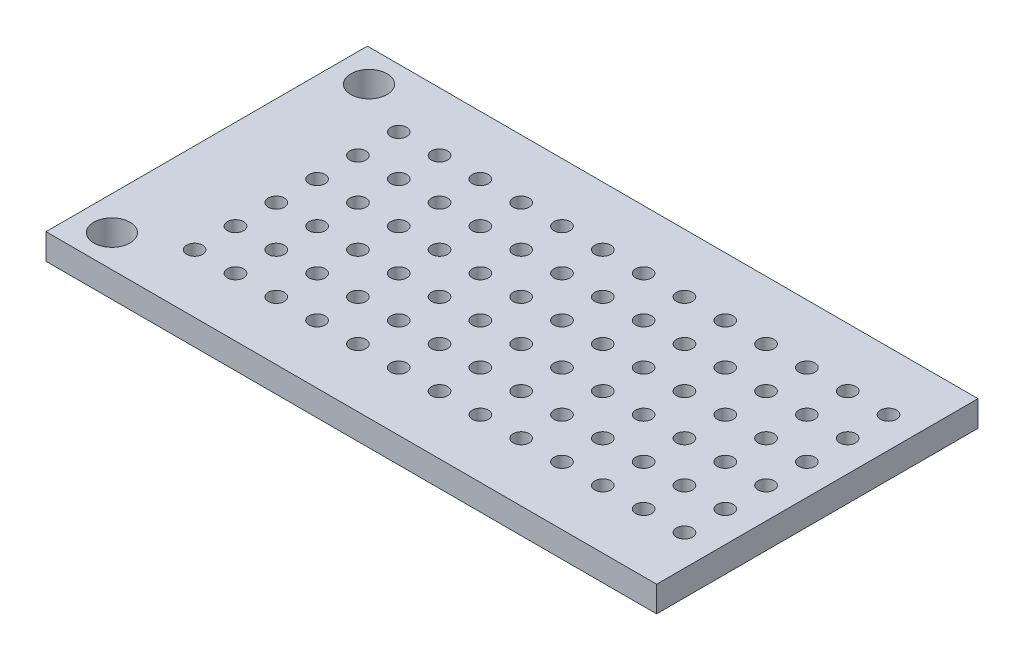
SolidWorks part; units mm, degrees
ref_plane "Front Plane" through (0, 0, 0) normal (0, 0, 1) x (1, 0, 0)
ref_plane "Top Plane" through (0, 0, 0) normal (0, 1, 0) x (1, 0, 0)
ref_plane "Right Plane" through (0, 0, 0) normal (1, 0, 0) x (0, 0, -1)
sketch "Sketch1" plane through (0, 0, 0) normal (0, 1, 0) x (1, 0, 0)
  line L1 (0, 0) -> (38, 0)
  line L2 (0, 0) -> (0, 20)
  line L3 (0, 20) -> (38, 20)
  line L4 (38, 0) -> (38, 20)
  dimension "D1" = 20
  dimension "D2" = 38
extrude "Boss-Extrude1" add sketch "Sketch1" along normal blind 1.6
sketch "Sketch2" plane through (0, 1.6, 0) normal (0, 1, 0) x (1, 0, 0)
  line L0 (2.1, 2) -> (2.1, 0) construction
  line L1 (0, 0) -> (38, 0) construction
  line L2 (2.1, 18) -> (2.1, 20) construction
  line L3 (38, 20) -> (0, 20) construction
  line L4 (0, 20) -> (0, 0) construction
  circle A0 centre (2.1, 18) radius 1.125
  circle A1 centre (2.1, 2) radius 1.125
  dimension "D1" = 2.25
  dimension "D2" = 2.25
  dimension "D3" = 16
  dimension "D4" = 2.1
sketch "Sketch3" plane through (0, 1.6, 0) normal (0, 1, 0) x (1, 0, 0)
  line L0 (0, 20) -> (0, 0) construction
  line L1 (5.6, 16.35) -> (5.6, 20) construction
  line L2 (38, 20) -> (0, 20) construction
  line L3 (5.6, 3.65) -> (5.6, 0) construction
  line L4 (0, 0) -> (38, 0) construction
  circle A0 centre (5.6, 16.35) radius 0.5
  circle A1 centre (8.14, 16.35) radius 0.5
  circle A2 centre (10.68, 16.35) radius 0.5
  circle A3 centre (13.22, 16.35) radius 0.5
  circle A4 centre (15.76, 16.35) radius 0.5
  circle A5 centre (18.3, 16.35) radius 0.5
  circle A6 centre (20.84, 16.35) radius 0.5
  circle A7 centre (23.38, 16.35) radius 0.5
  circle A8 centre (25.92, 16.35) radius 0.5
  circle A9 centre (28.46, 16.35) radius 0.5
  circle A10 centre (31, 16.35) radius 0.5
  circle A11 centre (33.54, 16.35) radius 0.5
  circle A12 centre (36.08, 16.35) radius 0.5
  circle A13 centre (8.14, 13.81) radius 0.5
  circle A14 centre (10.68, 13.81) radius 0.5
  circle A15 centre (13.22, 13.81) radius 0.5
  circle A16 centre (15.76, 13.81) radius 0.5
  circle A17 centre (18.3, 13.81) radius 0.5
  circle A18 centre (20.84, 13.81) radius 0.5
  circle A19 centre (23.38, 13.81) radius 0.5
  circle A20 centre (25.92, 13.81) radius 0.5
  circle A21 centre (28.46, 13.81) radius 0.5
  circle A22 centre (31, 13.81) radius 0.5
  circle A23 centre (33.54, 13.81) radius 0.5
  circle A24 centre (36.08, 13.81) radius 0.5
  circle A25 centre (8.14, 11.27) radius 0.5
  circle A26 centre (10.68, 11.27) radius 0.5
  circle A27 centre (13.22, 11.27) radius 0.5
  circle A28 centre (15.76, 11.27) radius 0.5
  circle A29 centre (18.3, 11.27) radius 0.5
  circle A30 centre (20.84, 11.27) radius 0.5
  circle A31 centre (23.38, 11.27) radius 0.5
  circle A32 centre (25.92, 11.27) radius 0.5
  circle A33 centre (28.46, 11.27) radius 0.5
  circle A34 centre (31, 11.27) radius 0.5
  circle A35 centre (33.54, 11.27) radius 0.5
  circle A36 centre (36.08, 11.27) radius 0.5
  circle A37 centre (8.14, 8.73) radius 0.5
  circle A38 centre (10.68, 8.73) radius 0.5
  circle A39 centre (13.22, 8.73) radius 0.5
  circle A40 centre (15.76, 8.73) radius 0.5
  circle A41 centre (18.3, 8.73) radius 0.5
  circle A42 centre (20.84, 8.73) radius 0.5
  circle A43 centre (23.38, 8.73) radius 0.5
  circle A44 centre (25.92, 8.73) radius 0.5
  circle A45 centre (28.46, 8.73) radius 0.5
  circle A46 centre (31, 8.73) radius 0.5
  circle A47 centre (33.54, 8.73) radius 0.5
  circle A48 centre (36.08, 8.73) radius 0.5
  circle A49 centre (8.14, 6.19) radius 0.5
  circle A50 centre (10.68, 6.19) radius 0.5
  circle A51 centre (13.22, 6.19) radius 0.5
  circle A52 centre (15.76, 6.19) radius 0.5
  circle A53 centre (18.3, 6.19) radius 0.5
  circle A54 centre (20.84, 6.19) radius 0.5
  circle A55 centre (23.38, 6.19) radius 0.5
  circle A56 centre (25.92, 6.19) radius 0.5
  circle A57 centre (28.46, 6.19) radius 0.5
  circle A58 centre (31, 6.19) radius 0.5
  circle A59 centre (33.54, 6.19) radius 0.5
  circle A60 centre (36.08, 6.19) radius 0.5
  circle A61 centre (8.14, 3.65) radius 0.5
  circle A62 centre (10.68, 3.65) radius 0.5
  circle A63 centre (13.22, 3.65) radius 0.5
  circle A64 centre (15.76, 3.65) radius 0.5
  circle A65 centre (18.3, 3.65) radius 0.5
  circle A66 centre (20.84, 3.65) radius 0.5
  circle A67 centre (23.38, 3.65) radius 0.5
  circle A68 centre (25.92, 3.65) radius 0.5
  circle A69 centre (28.46, 3.65) radius 0.5
  circle A70 centre (31, 3.65) radius 0.5
  circle A71 centre (33.54, 3.65) radius 0.5
  circle A72 centre (36.08, 3.65) radius 0.5
  circle A73 centre (5.6, 13.81) radius 0.5
  circle A74 centre (5.6, 11.27) radius 0.5
  circle A75 centre (5.6, 8.73) radius 0.5
  circle A76 centre (5.6, 6.19) radius 0.5
  circle A77 centre (5.6, 3.65) radius 0.5
  point P164 (0, 0)
  point P165 (8.4091, 3.6522)
  point P166 (10.0073, 3.719)
  point P167 (0, 0)
  point P168 (8.14, 3.65)
  point P169 (8.14, 8.73)
  dimension "D1" = 1
  dimension "D4" = 5.6
  dimension "D5" = 2.54
  dimension "D6" = 2.54
  dimension "D2" = 13
  dimension "D3" = 6
extrude "Cut-Extrude1" cut sketch "Sketch2" against normal through all
extrude "Cut-Extrude2" cut sketch "Sketch3" against normal through all
